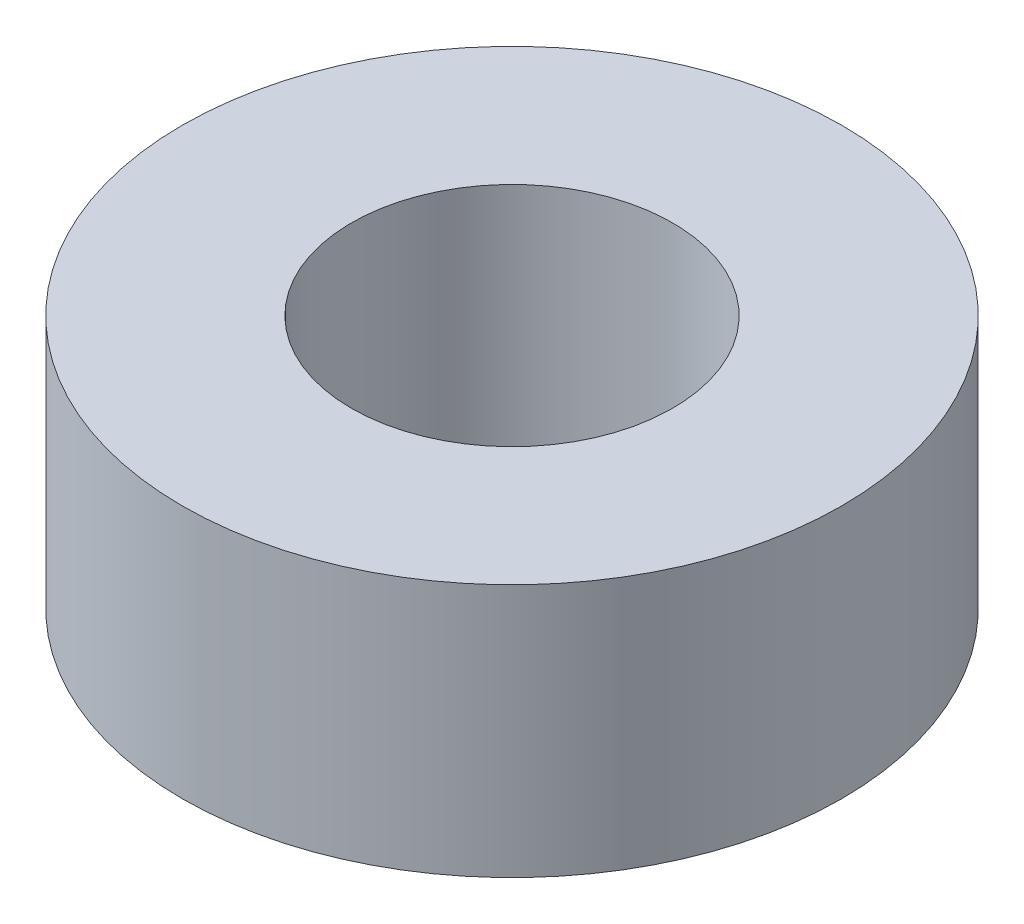
SolidWorks part; units mm, degrees
ref_plane "前视基准面" through (0, 0, 0) normal (0, 0, 1) x (1, 0, 0)
ref_plane "上视基准面" through (0, 0, 0) normal (0, 1, 0) x (1, 0, 0)
ref_plane "右视基准面" through (0, 0, 0) normal (1, 0, 0) x (0, 0, -1)
other "Configuration Table"
sketch "草图1" plane through (0, 0, 0) normal (0, 1, 0) x (1, 0, 0)
  circle A0 centre (0, 0) radius 1.9
  dimension "D1" = 3.8
extrude "拉伸-薄壁1" add sketch "草图1" along normal blind 3 thin
